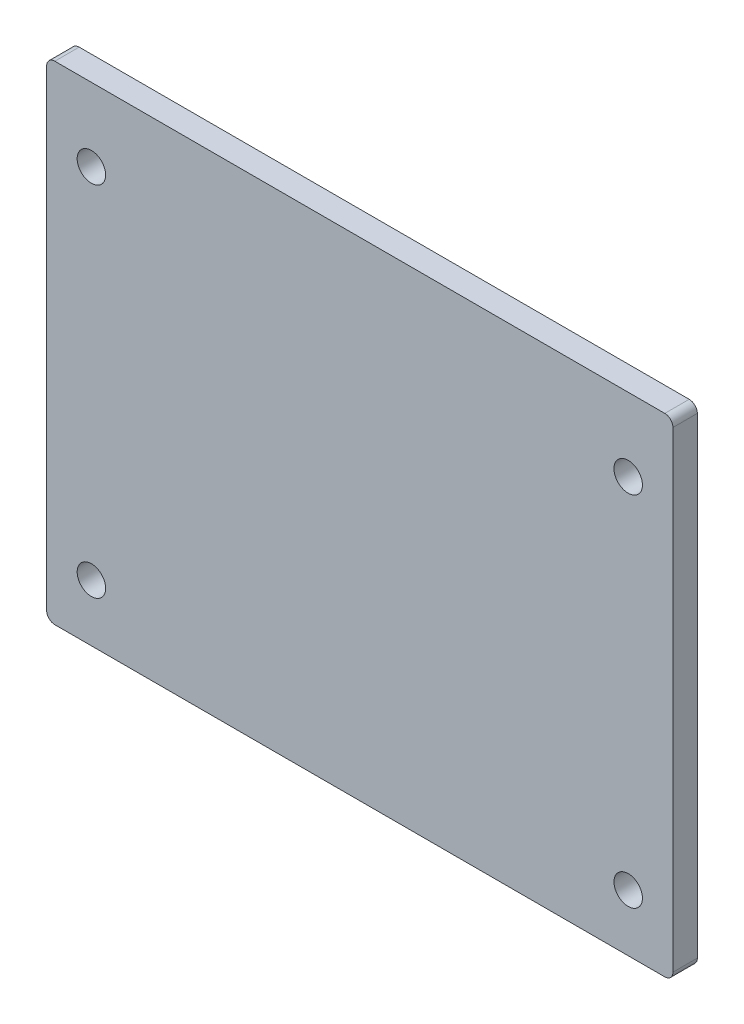
SolidWorks part; units mm, degrees
ref_plane "Front Plane" through (0, 0, 0) normal (0, 0, 1) x (1, 0, 0)
ref_plane "Top Plane" through (0, 0, 0) normal (0, 1, 0) x (1, 0, 0)
ref_plane "Right Plane" through (0, 0, 0) normal (1, 0, 0) x (0, 0, -1)
sketch "Sketch1" plane through (0, 0, 0) normal (0, 0, 1) x (1, 0, 0)
  line L1 (38.5, -30) -> (-38.5, -30)
  line L2 (38.5, -30) -> (38.5, 30)
  line L3 (38.5, 30) -> (-38.5, 30)
  line L4 (-38.5, -30) -> (-38.5, 30)
  circle A0 centre (33, -23) radius 1.75
  circle A1 centre (-33, -23) radius 1.75
  circle A2 centre (33, 21) radius 1.75
  circle A3 centre (-33, 21) radius 1.75
extrude "Boss-Extrude1" add sketch "Sketch1" along normal blind 3
fillet "Fillet1" radius 1 4 edges at (38.5, 30, 1.5) (38.5, -30, 1.5) (-38.5, -30, 1.5) (-38.5, 30, 1.5)
